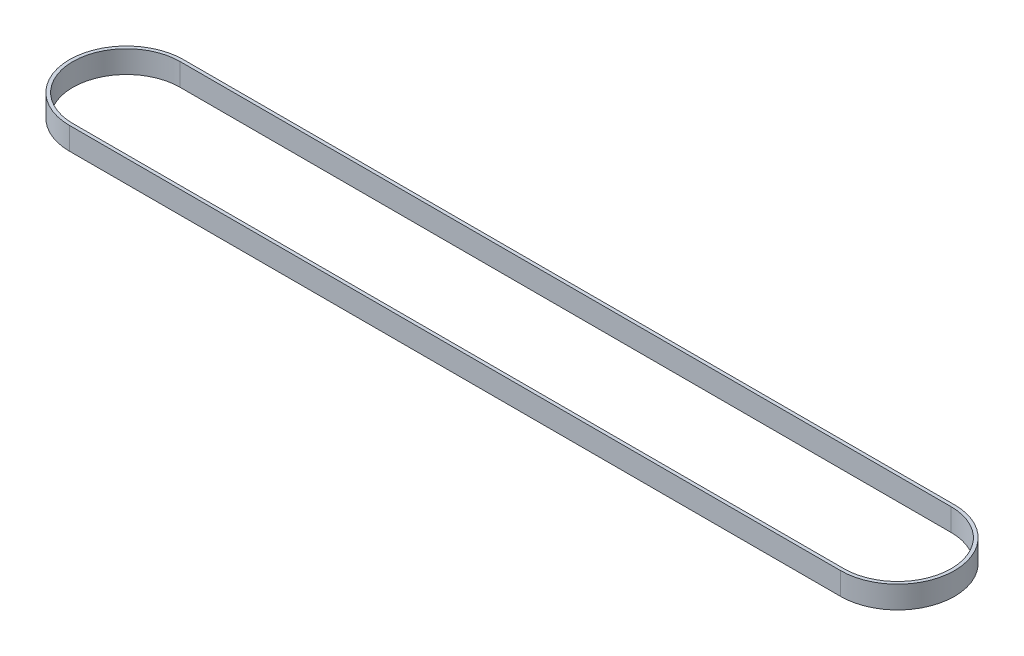
SolidWorks part; units mm, degrees
material "BUTYL"
ref_plane "Front Plane" through (0, 0, 0) normal (0, 0, 1) x (1, 0, 0)
ref_plane "Top Plane" through (0, 0, 0) normal (0, 1, 0) x (1, 0, 0)
ref_plane "Right Plane" through (0, 0, 0) normal (1, 0, 0) x (0, 0, -1)
sketch "Sketch1" plane through (0, 0, 0) normal (0, 1, 0) x (1, 0, 0)
  line L0 (-115.3215, -24) -> (229.6785, -24)
  line L1 (-115.3215, 24) -> (229.6785, 24)
  line L2 (-115.3215, 25.5) -> (229.6785, 25.5)
  line L3 (-115.3215, -25.5) -> (229.6785, -25.5)
  arc A0 (-115.3215, 24) -> (-115.3215, -24) centre (-115.3215, 0) ccw
  arc A1 (229.6785, -24) -> (229.6785, 24) centre (229.6785, 0) ccw
  arc A2 (229.6785, -25.5) -> (229.6785, 25.5) centre (229.6785, 0) ccw
  arc A3 (-115.3215, 25.5) -> (-115.3215, -25.5) centre (-115.3215, 0) ccw
  dimension "D1" = 48
  dimension "D2" = 48
  dimension "D3" = 345
  dimension "D4" = 1.5
extrude "Boss-Extrude1" add sketch "Sketch1" along normal blind 10
